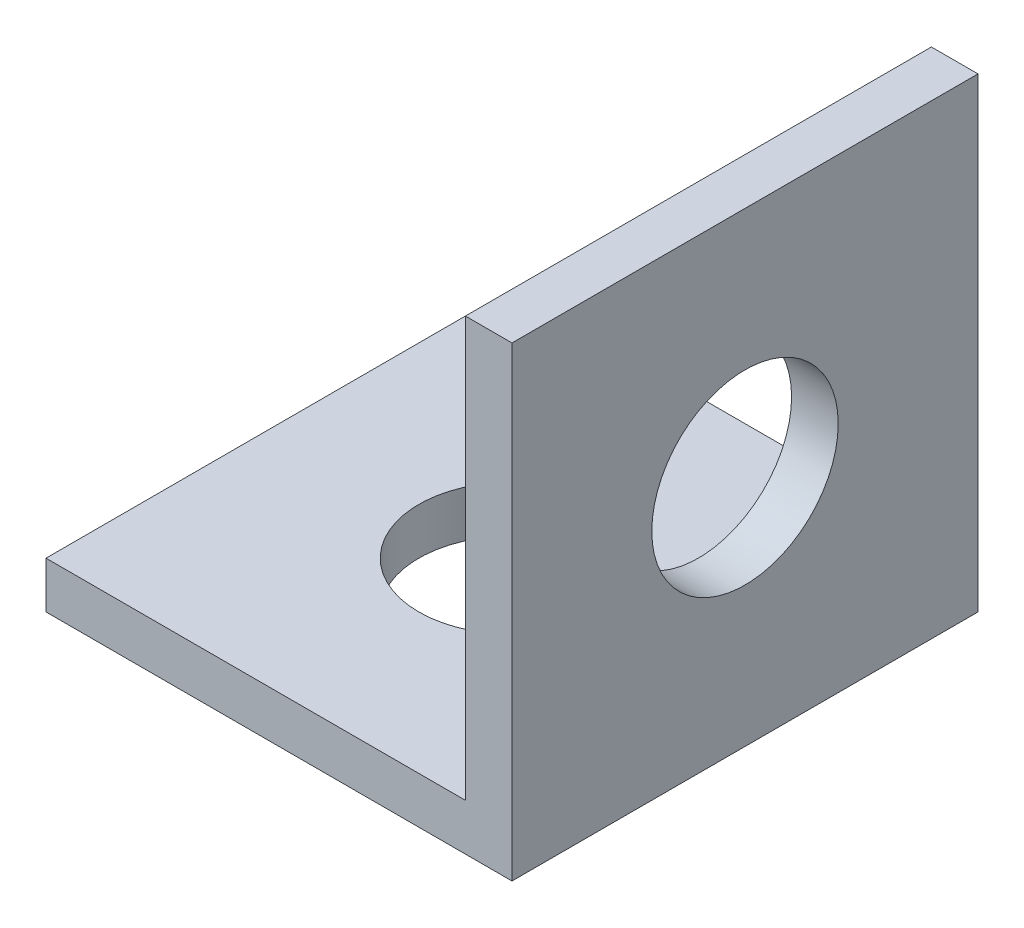
SolidWorks part; units mm, degrees
ref_plane "Face" through (0, 0, 0) normal (0, 0, 1) x (1, 0, 0)
ref_plane "Dessus" through (0, 0, 0) normal (0, 1, 0) x (1, 0, 0)
ref_plane "Droite" through (0, 0, 0) normal (1, 0, 0) x (0, 0, -1)
sketch "Esquisse1" plane through (0, 0, 0) normal (0, 1, 0) x (1, 0, 0)
  line L0 (5, 10) -> (5, 0) construction
  line L1 (0, 0) -> (10, 0)
  line L2 (0, 0) -> (0, 10)
  line L3 (0, 10) -> (10, 10)
  line L4 (10, 0) -> (10, 10)
  line L5 (0, 5) -> (10, 5) construction
  circle A0 centre (5, 5) radius 2
  dimension "D3" = 4
  dimension "D1" = 10
  dimension "D2" = 10
extrude "Extrusion1" add sketch "Esquisse1" along normal blind 1
sketch "Esquisse2" plane through (0, 1, 0) normal (0, 1, 0) x (1, 0, 0)
  line L0 (10, 10) -> (0, 10) construction
  line L1 (10, 0) -> (9, 0)
  line L2 (10, 0) -> (10, 10)
  line L3 (10, 10) -> (9, 10)
  line L4 (9, 0) -> (9, 10)
  dimension "D1" = 1
extrude "Extrusion2" add sketch "Esquisse2" along normal blind 9
sketch "Esquisse3" plane through (10, 0, 0) normal (1, 0, 0) x (0, 0, -1)
  line L0 (5, 10) -> (5, 0) construction
  line L1 (0, 10) -> (10, 10) construction
  line L2 (0, 0) -> (10, 0) construction
  line L3 (10, 5) -> (0, 5) construction
  line L6 (10, 10) -> (0, 10) construction
  circle A0 centre (5, 5) radius 2
  dimension "D1" = 4
  dimension "D2" = 5
extrude "Extrusion3" cut sketch "Esquisse3" against normal up to next
